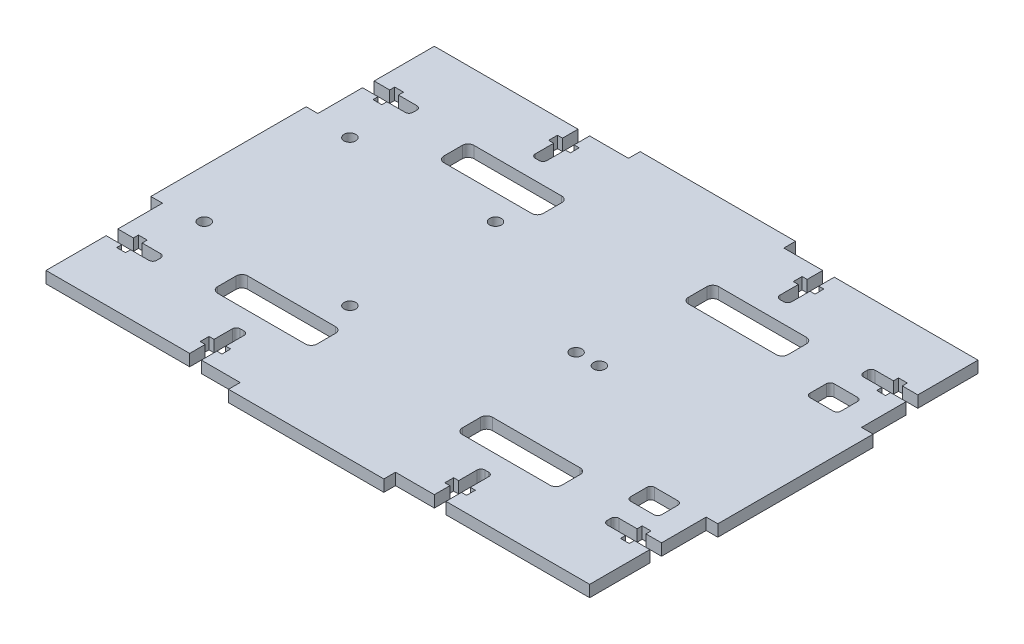
SolidWorks part; units mm, degrees
material "Acrylic (Medium-high impact)"
ref_plane "Plano frontal" through (0, 0, 0) normal (0, 0, 1) x (1, 0, 0)
ref_plane "Plano superior" through (0, 0, 0) normal (0, 1, 0) x (1, 0, 0)
ref_plane "Plano direito" through (0, 0, 0) normal (1, 0, 0) x (0, 0, -1)
sketch "Esboço1" plane through (0, 0, 0) normal (0, 1, 0) x (1, 0, 0)
  line L1 (-70, -50) -> (70, -50)
  line L2 (-70, -50) -> (-70, 50)
  line L3 (-70, 50) -> (70, 50)
  line L4 (70, -50) -> (70, 50)
  line L5 (-70, -50) -> (70, 50) construction
  line L6 (-70, 50) -> (70, -50) construction
  point P0 (0, 0)
  dimension "D1" = 140
  dimension "D2" = 100
extrude "Ressalto-extrusão1" add sketch "Esboço1" along normal mid plane 3
sketch "Esboço4" plane through (0, 1.5, 0) normal (0, 1, 0) x (1, 0, 0)
  line L5 (-70, 50) -> (-70, -50) construction
  line L6 (-70, 20) -> (-73, 20)
  line L7 (-70, 20) -> (-70, -20)
  line L8 (-70, -20) -> (-73, -20)
  line L9 (-73, 20) -> (-73, -20)
  line L16 (-20, 50) -> (20, 50)
  line L17 (-20, 50) -> (-20, 53)
  line L18 (-20, 53) -> (20, 53)
  line L19 (20, 50) -> (20, 53)
  line L20 (70, 50) -> (-70, 50) construction
  line L21 (-1.65, 0) -> (1.65, 0) construction
  line L22 (20, -50) -> (20, -53)
  line L23 (-20, -53) -> (20, -53)
  line L24 (-20, -50) -> (-20, -53)
  line L25 (-20, -50) -> (20, -50)
  line L26 (0, -1.65) -> (0, 1.65) construction
  line L27 (73, 20) -> (73, -20)
  line L28 (70, -20) -> (73, -20)
  line L29 (70, 20) -> (70, -20)
  line L30 (70, 20) -> (73, 20)
  point P14 (-73, 0)
  point P28 (0, 53)
  dimension "D3" = 3
  dimension "D4" = 40
extrude "Ressalto-extrusão2" add sketch "Esboço4" against normal through all
sketch "Esboço2" plane through (0, 1.5, 0) normal (0, 1, 0) x (1, 0, 0)
  line L0 (-33, -43.73) -> (-33, -39)
  line L13 (-30, -46) -> (-28.7, -46)
  line L14 (-30, -43.73) -> (-30, -39)
  line L27 (-70, -50) -> (-20, -50) construction
  line L28 (-33, -50) -> (-30, -50)
  line L29 (-33, -50) -> (-33, -46)
  line L30 (-32, -38) -> (-31, -38)
  line L31 (-30, -50) -> (-30, -46)
  line L33 (-30, -43.73) -> (-28.7, -43.73)
  line L34 (-34.3, -46) -> (-33, -46)
  line L35 (-34.3, -46) -> (-34.3, -43.73)
  line L36 (-34.3, -43.73) -> (-33, -43.73)
  line L37 (-28.7, -46) -> (-28.7, -43.73)
  line L38 (-20, -50) -> (-20, -53) construction
  line L51 (-1.65, 0) -> (1.65, 0) construction
  line L52 (-28.7, 46) -> (-28.7, 43.73)
  line L53 (-34.3, 43.73) -> (-33, 43.73)
  line L54 (-34.3, 46) -> (-34.3, 43.73)
  line L55 (-34.3, 46) -> (-33, 46)
  line L56 (-30, 43.73) -> (-28.7, 43.73)
  line L57 (-30, 50) -> (-30, 46)
  line L58 (-32, 38) -> (-31, 38)
  line L59 (-33, 50) -> (-33, 46)
  line L60 (-33, 50) -> (-30, 50)
  line L61 (-30, 43.73) -> (-30, 39)
  line L62 (-30, 46) -> (-28.7, 46)
  line L63 (-33, 43.73) -> (-33, 39)
  line L64 (0, -1.65) -> (0, 1.65) construction
  line L65 (33, 43.73) -> (33, 39)
  line L66 (30, 46) -> (28.7, 46)
  line L67 (30, 43.73) -> (30, 39)
  line L68 (33, 50) -> (30, 50)
  line L69 (33, 50) -> (33, 46)
  line L70 (32, 38) -> (31, 38)
  line L71 (30, 50) -> (30, 46)
  line L72 (30, 43.73) -> (28.7, 43.73)
  line L73 (34.3, 46) -> (33, 46)
  line L74 (34.3, 46) -> (34.3, 43.73)
  line L75 (34.3, 43.73) -> (33, 43.73)
  line L76 (28.7, 46) -> (28.7, 43.73)
  line L77 (28.7, -46) -> (28.7, -43.73)
  line L78 (34.3, -43.73) -> (33, -43.73)
  line L79 (34.3, -46) -> (34.3, -43.73)
  line L80 (34.3, -46) -> (33, -46)
  line L81 (30, -43.73) -> (28.7, -43.73)
  line L82 (30, -50) -> (30, -46)
  line L83 (32, -38) -> (31, -38)
  line L84 (33, -50) -> (33, -46)
  line L85 (33, -50) -> (30, -50)
  line L86 (30, -43.73) -> (30, -39)
  line L87 (30, -46) -> (28.7, -46)
  line L88 (33, -43.73) -> (33, -39)
  arc A0 (-31, -38) -> (-30, -39) centre (-31, -39) cw
  arc A1 (-33, -39) -> (-32, -38) centre (-32, -39) cw
  arc A2 (-33, 39) -> (-32, 38) centre (-32, 39) ccw
  arc A3 (-31, 38) -> (-30, 39) centre (-31, 39) ccw
  arc A4 (31, 38) -> (30, 39) centre (31, 39) cw
  arc A5 (33, 39) -> (32, 38) centre (32, 39) cw
  arc A6 (33, -39) -> (32, -38) centre (32, -39) ccw
  arc A7 (31, -38) -> (30, -39) centre (31, -39) ccw
  point P20 (-33, -38)
  point P39 (-33, 38)
  point P74 (33, 38)
  point P75 (33, -38)
  dimension "D8" = 1
  dimension "D1" = 10
  dimension "D2" = 3
  dimension "D3" = 12
  dimension "D4" = 4
  dimension "D5" = 1.3
  dimension "D6" = 2.27
  dimension "D7" = 1.3
extrude "Corte-extrusão1" cut sketch "Esboço2" against normal through all
sketch "Esboço7" plane through (0, 1.5, 0) normal (0, 1, 0) x (1, 0, 0)
  line L0 (-70, -20) -> (-70, -50) construction
  line L1 (-70, -31.5) -> (-66, -31.5)
  line L2 (-70, -31.5) -> (-70, -34.5)
  line L3 (-70, -34.5) -> (-66, -34.5)
  line L4 (-58, -32.5) -> (-58, -33.5)
  line L6 (-66, -30.2) -> (-63.73, -30.2)
  line L7 (-66, -30.2) -> (-66, -31.5)
  line L8 (-66, -35.8) -> (-63.73, -35.8)
  line L9 (-63.73, -30.2) -> (-63.73, -31.5)
  line L10 (-63.73, -31.5) -> (-59, -31.5)
  line L11 (-63.73, -34.5) -> (-59, -34.5)
  line L12 (-63.73, -34.5) -> (-63.73, -35.8)
  line L13 (-66, -34.5) -> (-66, -35.8)
  line L14 (-73, -20) -> (-70, -20) construction
  line L15 (0, -1.65) -> (0, 1.65) construction
  line L17 (66, -34.5) -> (66, -35.8)
  line L18 (63.73, -34.5) -> (63.73, -35.8)
  line L19 (63.73, -34.5) -> (59, -34.5)
  line L20 (63.73, -31.5) -> (59, -31.5)
  line L21 (63.73, -30.2) -> (63.73, -31.5)
  line L22 (66, -35.8) -> (63.73, -35.8)
  line L23 (66, -30.2) -> (66, -31.5)
  line L24 (66, -30.2) -> (63.73, -30.2)
  line L25 (58, -32.5) -> (58, -33.5)
  line L26 (70, -34.5) -> (66, -34.5)
  line L27 (70, -31.5) -> (70, -34.5)
  line L28 (70, -31.5) -> (66, -31.5)
  line L29 (-1.65, 0) -> (1.65, 0) construction
  line L32 (70, 31.5) -> (66, 31.5)
  line L33 (70, 31.5) -> (70, 34.5)
  line L34 (70, 34.5) -> (66, 34.5)
  line L35 (58, 32.5) -> (58, 33.5)
  line L36 (66, 30.2) -> (63.73, 30.2)
  line L37 (66, 30.2) -> (66, 31.5)
  line L38 (66, 35.8) -> (63.73, 35.8)
  line L39 (63.73, 30.2) -> (63.73, 31.5)
  line L40 (63.73, 31.5) -> (59, 31.5)
  line L41 (63.73, 34.5) -> (59, 34.5)
  line L42 (63.73, 34.5) -> (63.73, 35.8)
  line L43 (66, 34.5) -> (66, 35.8)
  line L44 (-66, 34.5) -> (-66, 35.8)
  line L45 (-63.73, 34.5) -> (-63.73, 35.8)
  line L46 (-63.73, 34.5) -> (-59, 34.5)
  line L47 (-63.73, 31.5) -> (-59, 31.5)
  line L48 (-63.73, 30.2) -> (-63.73, 31.5)
  line L49 (-66, 35.8) -> (-63.73, 35.8)
  line L50 (-66, 30.2) -> (-66, 31.5)
  line L51 (-66, 30.2) -> (-63.73, 30.2)
  line L52 (-58, 32.5) -> (-58, 33.5)
  line L53 (-70, 34.5) -> (-66, 34.5)
  line L54 (-70, 31.5) -> (-70, 34.5)
  line L55 (-70, 31.5) -> (-66, 31.5)
  arc A0 (59, -34.5) -> (58, -33.5) centre (59, -33.5) cw
  arc A1 (59, -31.5) -> (58, -32.5) centre (59, -32.5) ccw
  arc A2 (58, 32.5) -> (59, 31.5) centre (59, 32.5) ccw
  arc A3 (58, 33.5) -> (59, 34.5) centre (59, 33.5) cw
  arc A4 (-59, 34.5) -> (-58, 33.5) centre (-59, 33.5) cw
  arc A5 (-59, 31.5) -> (-58, 32.5) centre (-59, 32.5) ccw
  arc A6 (-59, -31.5) -> (-58, -32.5) centre (-59, -32.5) cw
  arc A7 (-59, -34.5) -> (-58, -33.5) centre (-59, -33.5) ccw
  point P22 (58, -34.5)
  point P68 (58, -31.5)
  point P71 (58, 31.5)
  point P74 (58, 34.5)
  point P77 (-58, 34.5)
  point P80 (-58, 31.5)
  point P83 (-58, -31.5)
  point P86 (-58, -34.5)
  dimension "D8" = 1
  dimension "D1" = 3
  dimension "D2" = 12
  dimension "D3" = 2.27
  dimension "D4" = 4
  dimension "D5" = 1.3
  dimension "D6" = 11.5
  dimension "D7" = 1.3
extrude "Corte-extrusão4" cut sketch "Esboço7" against normal through all
sketch "Esboço13" plane through (0, -1.5, 0) normal (0, -1, 0) x (-1, 0, 0)
  line L0 (60.5, 18.75) -> (60.5, -18.75) construction
  line L2 (51.5, 50) -> (51.5, -50) construction
  line L3 (33, 50) -> (70, 50) construction
  line L4 (70, -50) -> (33, -50) construction
  line L6 (70, 31.5) -> (70, 20) construction
  circle A0 centre (60.5, -18.75) radius 1.5
  circle A1 centre (23, -18.75) radius 1.5
  circle A2 centre (60.5, 18.75) radius 1.5
  circle A3 centre (23, 18.75) radius 1.5
  point P10 (60.5, 0)
  dimension "D1" = 3
  dimension "D2" = 8
  dimension "D3" = 37.5
  dimension "D5" = 37.5
  dimension "D6" = 100
extrude "Corte-extrusão8" cut sketch "Esboço13" against normal through all both and the other way through all
sketch "Sketch3" plane through (0, 1.5, 0) normal (0, 1, 0) x (1, 0, 0)
  circle A0 centre (16.5, 0) radius 1.5
  circle A1 centre (22.5, 0) radius 1.5
  dimension "D1" = 3
  dimension "D2" = 3
  dimension "D3" = 16.5
extrude "Cut-Extrude2" cut sketch "Sketch3" against normal through all both and the other way through all
sketch "Sketch4" plane through (0, 0, 0) normal (0, 1, 0) x (1, 0, 0)
  line L0 (-1.65, 0) -> (1.65, 0) construction
  line L35 (-32, 38) -> (-31, 38) construction
  line L40 (-42.8, 33) -> (-20.2, 33)
  line L41 (73, 20) -> (70, 20) construction
  line L42 (56.73, 26.2) -> (62.73, 26.2)
  line L43 (55.73, 25.2) -> (55.73, 21)
  line L44 (56.73, 20) -> (62.73, 20)
  line L45 (63.73, 25.2) -> (63.73, 21)
  line L46 (-44.3, 31.5) -> (-44.3, 26.75)
  line L47 (63.73, 31.5) -> (63.73, 30.2) construction
  line L48 (63.73, 30.2) -> (66, 30.2) construction
  line L49 (63.73, -25.2) -> (63.73, -21)
  line L50 (56.73, -20) -> (62.73, -20)
  line L51 (55.73, -25.2) -> (55.73, -21)
  line L52 (56.73, -26.2) -> (62.73, -26.2)
  line L53 (-42.8, 25.25) -> (-20.2, 25.25)
  line L54 (-18.7, 31.5) -> (-18.7, 26.75)
  line L59 (-34.3, 46) -> (-34.3, 43.73) construction
  line L60 (-28.7, 43.73) -> (-28.7, 46) construction
  line L61 (0, -1.65) -> (0, 1.65) construction
  line L62 (18.7, 31.5) -> (18.7, 26.75)
  line L63 (42.8, 25.25) -> (20.2, 25.25)
  line L64 (44.3, 31.5) -> (44.3, 26.75)
  line L65 (42.8, 33) -> (20.2, 33)
  line L66 (42.8, -33) -> (20.2, -33)
  line L67 (44.3, -31.5) -> (44.3, -26.75)
  line L68 (42.8, -25.25) -> (20.2, -25.25)
  line L69 (18.7, -31.5) -> (18.7, -26.75)
  line L70 (-18.7, -31.5) -> (-18.7, -26.75)
  line L71 (-42.8, -25.25) -> (-20.2, -25.25)
  line L72 (-44.3, -31.5) -> (-44.3, -26.75)
  line L73 (-42.8, -33) -> (-20.2, -33)
  arc A21 (62.73, 26.2) -> (63.73, 25.2) centre (62.73, 25.2) cw
  arc A22 (62.73, 20) -> (63.73, 21) centre (62.73, 21) ccw
  arc A23 (55.73, 21) -> (56.73, 20) centre (56.73, 21) ccw
  arc A24 (56.73, 26.2) -> (55.73, 25.2) centre (56.73, 25.2) ccw
  arc A25 (56.73, -26.2) -> (55.73, -25.2) centre (56.73, -25.2) cw
  arc A26 (55.73, -21) -> (56.73, -20) centre (56.73, -21) cw
  arc A27 (62.73, -20) -> (63.73, -21) centre (62.73, -21) cw
  arc A28 (62.73, -26.2) -> (63.73, -25.2) centre (62.73, -25.2) ccw
  circle A30 centre (-23, 18.75) radius 1.5 construction
  arc A31 (-20.2, 25.25) -> (-18.7, 26.75) centre (-20.2, 26.75) ccw
  arc A32 (-20.2, 33) -> (-18.7, 31.5) centre (-20.2, 31.5) cw
  arc A33 (-42.8, 33) -> (-44.3, 31.5) centre (-42.8, 31.5) ccw
  arc A34 (-44.3, 26.75) -> (-42.8, 25.25) centre (-42.8, 26.75) ccw
  arc A35 (44.3, 26.75) -> (42.8, 25.25) centre (42.8, 26.75) cw
  arc A36 (42.8, 33) -> (44.3, 31.5) centre (42.8, 31.5) cw
  arc A37 (20.2, 33) -> (18.7, 31.5) centre (20.2, 31.5) ccw
  arc A38 (20.2, 25.25) -> (18.7, 26.75) centre (20.2, 26.75) cw
  arc A39 (20.2, -25.25) -> (18.7, -26.75) centre (20.2, -26.75) ccw
  arc A40 (20.2, -33) -> (18.7, -31.5) centre (20.2, -31.5) cw
  arc A41 (42.8, -33) -> (44.3, -31.5) centre (42.8, -31.5) ccw
  arc A42 (44.3, -26.75) -> (42.8, -25.25) centre (42.8, -26.75) ccw
  arc A43 (-44.3, -26.75) -> (-42.8, -25.25) centre (-42.8, -26.75) cw
  arc A44 (-42.8, -33) -> (-44.3, -31.5) centre (-42.8, -31.5) cw
  arc A45 (-20.2, -33) -> (-18.7, -31.5) centre (-20.2, -31.5) ccw
  arc A46 (-20.2, -25.25) -> (-18.7, -26.75) centre (-20.2, -26.75) cw
  point P75 (63.73, 26.2)
  point P82 (55.73, 26.2)
  point P95 (55.73, -26.2)
  point P96 (63.73, -26.2)
  dimension "D4" = 10
  dimension "D3" = 5
  dimension "D6" = 1.5
  dimension "D2" = 5
  dimension "D5" = 10
  dimension "D10" = 1
  dimension "D8" = 4
  dimension "D9" = 8
extrude "Cut-Extrude3" cut sketch "Sketch4" against normal through all both and the other way through all
